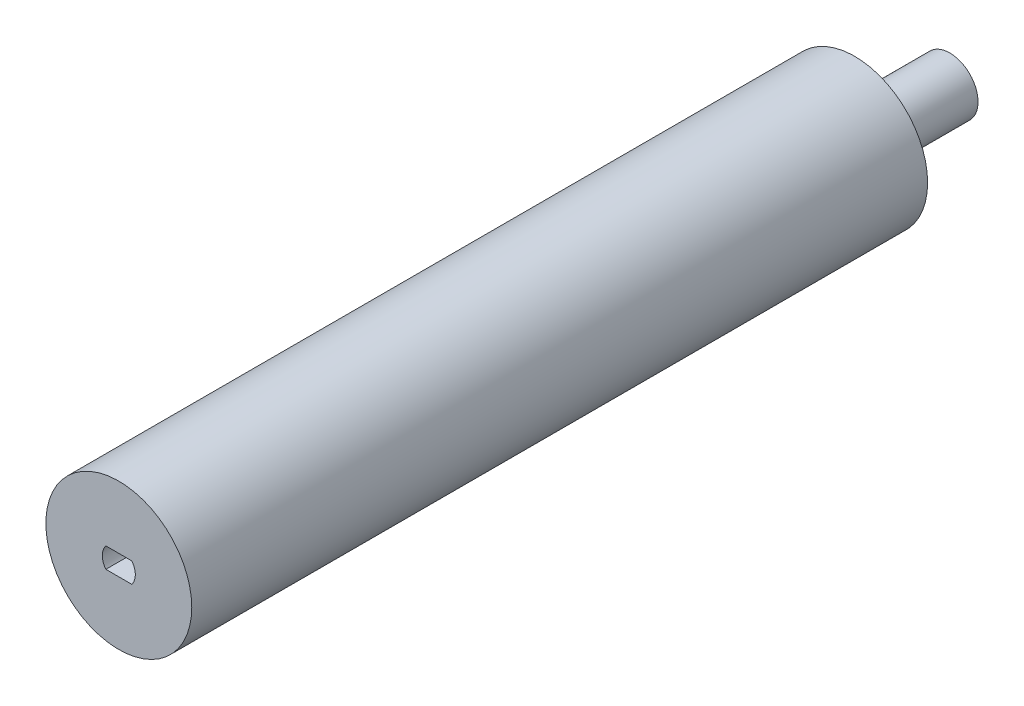
SolidWorks part; units mm, degrees
ref_plane "Front Plane" through (0, 0, 0) normal (0, 0, 1) x (1, 0, 0)
ref_plane "Top Plane" through (0, 0, 0) normal (0, 1, 0) x (1, 0, 0)
ref_plane "Right Plane" through (0, 0, 0) normal (1, 0, 0) x (0, 0, -1)
sketch "Sketch1" plane through (0, 0, 0) normal (0, 0, 1) x (1, 0, 0)
  line L10 (2.0511, -1.5674) -> (-2.0477, -1.5674)
  line L11 (2.0511, 1.6326) -> (-2.0477, 1.6326)
  arc A12 (-2.0477, 1.6326) -> (-2.0477, -1.5674) centre (0.0017, 0.0326) ccw
  arc A13 (2.0511, -1.5674) -> (2.0511, 1.6326) centre (0.0017, 0.0326) ccw
  point P8 (0, 1.5)
  point P11 (0, -1.5)
sketch "Sketch2" plane through (0, 0, 0) normal (0, 0, 1) x (1, 0, 0)
  circle A0 centre (0, 0) radius 11.5
  dimension "D1" = 23
extrude "Boss-Extrude1" add sketch "Sketch2" against normal blind 116
sketch "Sketch3" plane through (0, 0, -116) normal (0, 0, -1) x (-1, 0, 0)
  circle A0 centre (0, 0) radius 4.45
  dimension "D1" = 8.9
extrude "Boss-Extrude2" add sketch "Sketch3" along normal blind 15
extrude "Cut-Extrude1" cut sketch "Sketch1" against normal blind 10
